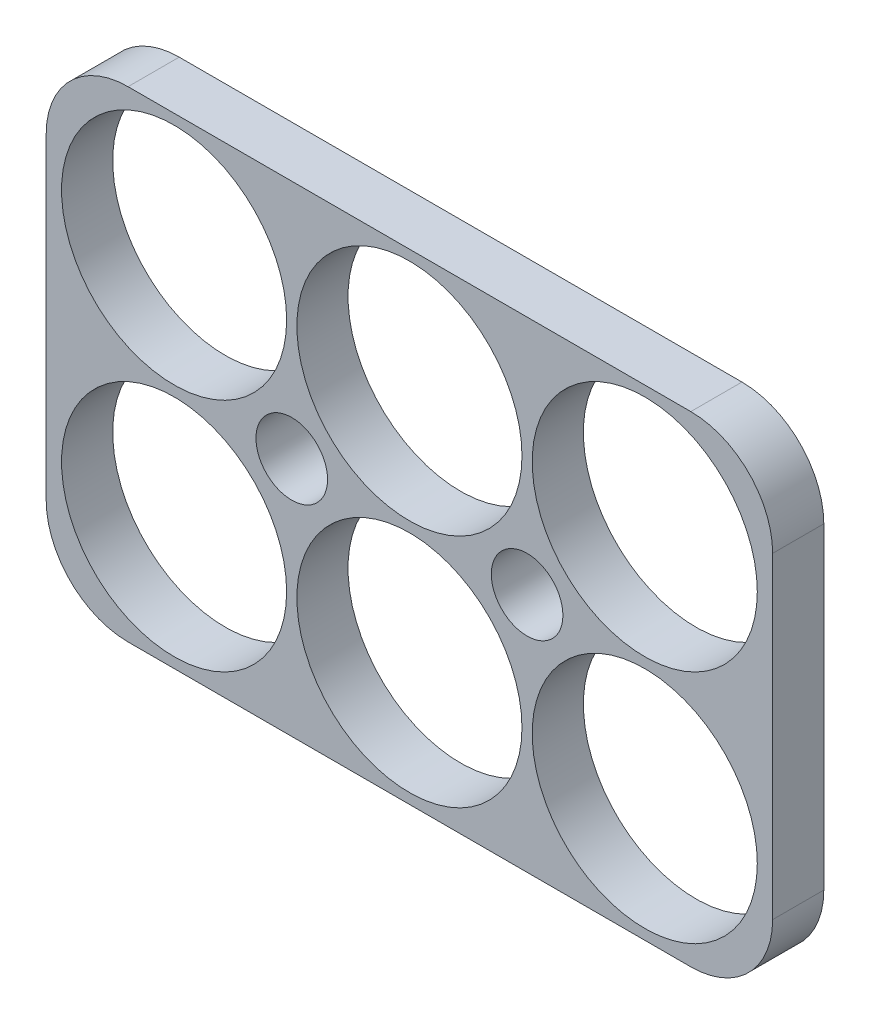
SolidWorks part; units mm, degrees
ref_plane "前视基准面" through (0, 0, 0) normal (0, 0, 1) x (1, 0, 0)
ref_plane "上视基准面" through (0, 0, 0) normal (0, 1, 0) x (1, 0, 0)
ref_plane "右视基准面" through (0, 0, 0) normal (1, 0, 0) x (0, 0, -1)
sketch "草图1" plane through (0, 0, 0) normal (0, 0, 1) x (1, 0, 0)
  line L1 (-35.5, 23.5) -> (35.5, 23.5)
  line L2 (-35.5, 23.5) -> (-35.5, -23.5)
  line L3 (-35.5, -23.5) -> (35.5, -23.5)
  line L4 (35.5, 23.5) -> (35.5, -23.5)
  line L5 (0, -23.5) -> (0, 23.5) construction
  line L6 (-35.5, 0) -> (35.5, 0) construction
  circle A0 centre (-23, 11.5) radius 11
  circle A1 centre (0, 11.5) radius 11
  circle A2 centre (23, 11.5) radius 11
  circle A3 centre (23, -11.5) radius 11
  circle A4 centre (0, -11.5) radius 11
  circle A5 centre (-23, -11.5) radius 11
  circle A6 centre (11.5, 0) radius 3.5
  circle A7 centre (-11.5, 0) radius 3.5
  point P0 (0, 0)
  dimension "D3" = 22
  dimension "D4" = 22
  dimension "D5" = 22
  dimension "D8" = 22
  dimension "D9" = 22
  dimension "D10" = 22
  dimension "D19" = 7
  dimension "D20" = 7
  dimension "D1" = 71
  dimension "D2" = 47
  dimension "D6" = 23
  dimension "D7" = 23
  dimension "D11" = 23
  dimension "D12" = 23
  dimension "D13" = 11.5
  dimension "D14" = 11.5
  dimension "D15" = 11.5
  dimension "D16" = 11.5
  dimension "D17" = 11.5
  dimension "D18" = 11.5
  dimension "D21" = 11.5
  dimension "D22" = 11.5
extrude "凸台-拉伸2" add sketch "草图1" against normal blind 5
fillet "圆角1" radius 8 4 edges at (-35.5, -23.5, -2.5) (35.5, -23.5, -2.5) (35.5, 23.5, -2.5) (-35.5, 23.5, -2.5)
